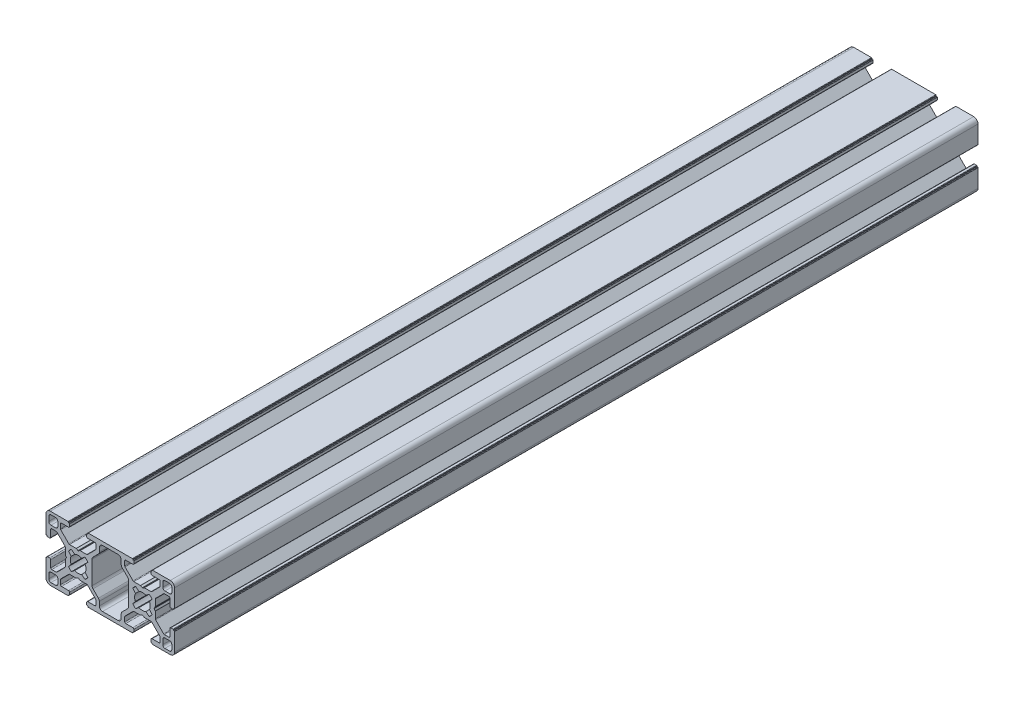
SolidWorks part; units mm, degrees
ref_plane "Front Plane" through (0, 0, 0) normal (0, 0, 1) x (1, 0, 0)
ref_plane "Top Plane" through (0, 0, 0) normal (0, 1, 0) x (1, 0, 0)
ref_plane "Right Plane" through (0, 0, 0) normal (1, 0, 0) x (0, 0, -1)
ref_plane "Plano1" through (0, 0, 1000) normal (0, 0, 1) x (1, 0, 0)
sketch "Croquis1" plane through (0, 0, 1000) normal (0, 0, 1) x (1, 0, 0)
  line L0 (-18.4, -4.5) -> (-18.4, -2.3)
  line L1 (-17.4, -1.3) -> (-15.2, -1.3)
  line L2 (-14.2, -2.3) -> (-14.2, -4.5)
  line L3 (-15.2, -5.5) -> (-17.4, -5.5)
  line L4 (-18.4, -27.7) -> (-18.4, -25.5)
  line L5 (-17.4, -24.5) -> (-15.2, -24.5)
  line L6 (-14.2, -25.5) -> (-14.2, -27.7)
  line L7 (-15.2, -28.7) -> (-17.4, -28.7)
  line L8 (35.8, -1.3) -> (38, -1.3)
  line L9 (39, -2.3) -> (39, -4.5)
  line L10 (38, -5.5) -> (35.8, -5.5)
  line L11 (34.8, -4.5) -> (34.8, -2.3)
  line L12 (35.8, -24.5) -> (38, -24.5)
  line L13 (39, -25.5) -> (39, -27.7)
  line L14 (38, -28.7) -> (35.8, -28.7)
  line L15 (34.8, -27.7) -> (34.8, -25.5)
  line L16 (-0.1816, -11.8641) -> (-1.4194, -13.3999)
  line L17 (-1.4194, -16.6001) -> (-0.1816, -18.1359)
  line L18 (-1.5453, -19.5053) -> (-3.0999, -18.2806)
  line L19 (-6.3001, -18.2806) -> (-7.8547, -19.5053)
  line L20 (-9.2184, -18.1359) -> (-7.9806, -16.6001)
  line L21 (-7.9806, -13.3999) -> (-9.2184, -11.8641)
  line L22 (-7.8547, -10.4947) -> (-6.3001, -11.7194)
  line L23 (-3.0999, -11.7194) -> (-1.5453, -10.4947)
  line L24 (20.7816, -18.1359) -> (22.0194, -16.6001)
  line L25 (22.0194, -13.3999) -> (20.7816, -11.8641)
  line L26 (22.1453, -10.4947) -> (23.6999, -11.7194)
  line L27 (26.9001, -11.7194) -> (28.4547, -10.4947)
  line L28 (29.8184, -11.8641) -> (28.5806, -13.3999)
  line L29 (28.5806, -16.6001) -> (29.8184, -18.1359)
  line L30 (28.4547, -19.5053) -> (26.9001, -18.2806)
  line L31 (23.6999, -18.2806) -> (22.1453, -19.5053)
  line L32 (18.7955, -9.6503) -> (18.7955, -20.3497)
  line L33 (18.3562, -21.4104) -> (15.8393, -23.9272)
  line L34 (15.4, -24.9879) -> (15.4, -26.85)
  line L35 (13.9, -28.35) -> (6.7, -28.35)
  line L36 (5.2, -26.85) -> (5.2, -24.9879)
  line L37 (4.7607, -23.9272) -> (2.2438, -21.4104)
  line L38 (1.8045, -20.3497) -> (1.8045, -9.6503)
  line L39 (2.2438, -8.5896) -> (4.7607, -6.0728)
  line L40 (5.2, -5.0121) -> (5.2, -3.15)
  line L41 (6.7, -1.65) -> (13.9, -1.65)
  line L42 (15.4, -3.15) -> (15.4, -5.0121)
  line L43 (15.8393, -6.0728) -> (18.3562, -8.5896)
  line L44 (-8.9, -0.5) -> (-9.2, -0.5)
  line L45 (-9.2, -0.5) -> (-9.2, -0.2)
  line L46 (-9.4, 0) -> (-17.7, 0)
  line L47 (-19.7, -2) -> (-19.7, -10.3)
  line L48 (-19.5, -10.5) -> (-19.2, -10.5)
  line L49 (-19.2, -10.5) -> (-19.2, -10.8)
  line L50 (-19, -11) -> (-18, -11)
  line L51 (-17.5, -10.5) -> (-17.5, -7.25)
  line L52 (-17, -6.75) -> (-14.9569, -6.75)
  line L53 (-14.6036, -6.8963) -> (-10.8466, -10.6491)
  line L54 (-10.7, -11.0028) -> (-10.7, -14.0468)
  line L55 (-10.6736, -14.1462) -> (-10.2417, -14.9006)
  line L56 (-10.2417, -15.0994) -> (-10.6736, -15.8538)
  line L57 (-10.7, -15.9532) -> (-10.7, -18.9972)
  line L58 (-10.8466, -19.3509) -> (-14.6036, -23.1037)
  line L59 (-14.9569, -23.25) -> (-17, -23.25)
  line L60 (-17.5, -22.75) -> (-17.5, -19.5)
  line L61 (-18, -19) -> (-19, -19)
  line L62 (-19.2, -19.2) -> (-19.2, -19.5)
  line L63 (-19.2, -19.5) -> (-19.5, -19.5)
  line L64 (-19.7, -19.7) -> (-19.7, -28)
  line L65 (-17.7, -30) -> (-9.4, -30)
  line L66 (-9.2, -29.8) -> (-9.2, -29.5)
  line L67 (-9.2, -29.5) -> (-8.9, -29.5)
  line L68 (-8.7, -29.3) -> (-8.7, -28.3)
  line L69 (-9.2, -27.8) -> (-12.45, -27.8)
  line L70 (-12.95, -27.3) -> (-12.95, -25.2571)
  line L71 (-12.8036, -24.9036) -> (-9.0509, -21.1509)
  line L72 (-8.6974, -21.0045) -> (-5.6536, -21.0045)
  line L73 (-5.5536, -20.9777) -> (-4.8, -20.5426)
  line L74 (-4.6, -20.5426) -> (-3.8464, -20.9777)
  line L75 (-3.7464, -21.0045) -> (-0.7026, -21.0045)
  line L76 (-0.3491, -21.1509) -> (3.4036, -24.9036)
  line L77 (3.55, -25.2571) -> (3.55, -27.3)
  line L78 (3.05, -27.8) -> (-0.2, -27.8)
  line L79 (-0.7, -28.3) -> (-0.7, -29.3)
  line L80 (-0.5, -29.5) -> (-0.2, -29.5)
  line L81 (-0.2, -29.5) -> (-0.2, -29.8)
  line L82 (0, -30) -> (20.6, -30)
  line L83 (20.8, -29.8) -> (20.8, -29.5)
  line L84 (20.8, -29.5) -> (21.1, -29.5)
  line L85 (21.3, -29.3) -> (21.3, -28.3)
  line L86 (20.8, -27.8) -> (17.55, -27.8)
  line L87 (17.05, -27.3) -> (17.05, -25.2571)
  line L88 (17.1964, -24.9036) -> (20.9491, -21.1509)
  line L89 (21.3026, -21.0045) -> (24.3464, -21.0045)
  line L90 (24.4464, -20.9777) -> (25.2, -20.5426)
  line L91 (25.4, -20.5426) -> (26.1536, -20.9777)
  line L92 (26.2536, -21.0045) -> (29.2974, -21.0045)
  line L93 (29.6509, -21.1509) -> (33.4036, -24.9036)
  line L94 (33.55, -25.2571) -> (33.55, -27.3)
  line L95 (33.05, -27.8) -> (29.8, -27.8)
  line L96 (29.3, -28.3) -> (29.3, -29.3)
  line L97 (29.5, -29.5) -> (29.8, -29.5)
  line L98 (29.8, -29.5) -> (29.8, -29.8)
  line L99 (30, -30) -> (38.3, -30)
  line L100 (40.3, -28) -> (40.3, -19.7)
  line L101 (40.1, -19.5) -> (39.8, -19.5)
  line L102 (39.8, -19.5) -> (39.8, -19.2)
  line L103 (39.6, -19) -> (38.6, -19)
  line L104 (38.1, -19.5) -> (38.1, -22.75)
  line L105 (37.6, -23.25) -> (35.5569, -23.25)
  line L106 (35.2036, -23.1037) -> (31.4466, -19.3509)
  line L107 (31.3, -18.9972) -> (31.3, -15.9532)
  line L108 (31.2736, -15.8538) -> (30.8417, -15.0994)
  line L109 (30.8417, -14.9006) -> (31.2736, -14.1462)
  line L110 (31.3, -14.0468) -> (31.3, -11.0028)
  line L111 (31.4466, -10.6491) -> (35.2036, -6.8963)
  line L112 (35.5569, -6.75) -> (37.6, -6.75)
  line L113 (38.1, -7.25) -> (38.1, -10.5)
  line L114 (38.6, -11) -> (39.6, -11)
  line L115 (39.8, -10.8) -> (39.8, -10.5)
  line L116 (39.8, -10.5) -> (40.1, -10.5)
  line L117 (40.3, -10.3) -> (40.3, -2)
  line L118 (38.3, 0) -> (30, 0)
  line L119 (29.8, -0.2) -> (29.8, -0.5)
  line L120 (29.8, -0.5) -> (29.5, -0.5)
  line L121 (29.3, -0.7) -> (29.3, -1.7)
  line L122 (29.8, -2.2) -> (33.05, -2.2)
  line L123 (33.55, -2.7) -> (33.55, -4.7429)
  line L124 (33.4036, -5.0964) -> (29.6509, -8.8491)
  line L125 (29.2974, -8.9955) -> (26.2536, -8.9955)
  line L126 (26.1536, -9.0223) -> (25.4, -9.4574)
  line L127 (25.2, -9.4574) -> (24.4464, -9.0223)
  line L128 (24.3464, -8.9955) -> (21.3026, -8.9955)
  line L129 (20.9491, -8.8491) -> (17.1964, -5.0964)
  line L130 (17.05, -4.7429) -> (17.05, -2.7)
  line L131 (17.55, -2.2) -> (20.8, -2.2)
  line L132 (21.3, -1.7) -> (21.3, -0.7)
  line L133 (21.1, -0.5) -> (20.8, -0.5)
  line L134 (20.8, -0.5) -> (20.8, -0.2)
  line L135 (20.6, 0) -> (0, 0)
  line L136 (-0.2, -0.2) -> (-0.2, -0.5)
  line L137 (-0.2, -0.5) -> (-0.5, -0.5)
  line L138 (-0.7, -0.7) -> (-0.7, -1.7)
  line L139 (-0.2, -2.2) -> (3.05, -2.2)
  line L140 (3.55, -2.7) -> (3.55, -4.7429)
  line L141 (3.4036, -5.0964) -> (-0.3491, -8.8491)
  line L142 (-0.7026, -8.9955) -> (-3.7464, -8.9955)
  line L143 (-3.8464, -9.0223) -> (-4.6, -9.4574)
  line L144 (-4.8, -9.4574) -> (-5.5536, -9.0223)
  line L145 (-5.6536, -8.9955) -> (-8.6974, -8.9955)
  line L146 (-9.0509, -8.8491) -> (-12.8036, -5.0964)
  line L147 (-12.95, -4.7429) -> (-12.95, -2.7)
  line L148 (-12.45, -2.2) -> (-9.2, -2.2)
  line L149 (-8.7, -1.7) -> (-8.7, -0.7)
  arc A0 (-17.4, -5.5) -> (-18.4, -4.5) centre (-17.4, -4.5) cw
  arc A1 (-18.4, -2.3) -> (-17.4, -1.3) centre (-17.4, -2.3) cw
  arc A2 (-15.2, -1.3) -> (-14.2, -2.3) centre (-15.2, -2.3) cw
  arc A3 (-14.2, -4.5) -> (-15.2, -5.5) centre (-15.2, -4.5) cw
  arc A4 (-17.4, -28.7) -> (-18.4, -27.7) centre (-17.4, -27.7) cw
  arc A5 (-18.4, -25.5) -> (-17.4, -24.5) centre (-17.4, -25.5) cw
  arc A6 (-15.2, -24.5) -> (-14.2, -25.5) centre (-15.2, -25.5) cw
  arc A7 (-14.2, -27.7) -> (-15.2, -28.7) centre (-15.2, -27.7) cw
  arc A8 (34.8, -2.3) -> (35.8, -1.3) centre (35.8, -2.3) cw
  arc A9 (38, -1.3) -> (39, -2.3) centre (38, -2.3) cw
  arc A10 (39, -4.5) -> (38, -5.5) centre (38, -4.5) cw
  arc A11 (35.8, -5.5) -> (34.8, -4.5) centre (35.8, -4.5) cw
  arc A12 (34.8, -25.5) -> (35.8, -24.5) centre (35.8, -25.5) cw
  arc A13 (38, -24.5) -> (39, -25.5) centre (38, -25.5) cw
  arc A14 (39, -27.7) -> (38, -28.7) centre (38, -27.7) cw
  arc A15 (35.8, -28.7) -> (34.8, -27.7) centre (35.8, -27.7) cw
  arc A16 (-1.5453, -10.4947) -> (-0.1816, -11.8641) centre (-4.7, -15) cw
  arc A17 (-1.4194, -13.3999) -> (-1.4194, -16.6001) centre (-4.7, -15) cw
  arc A18 (-0.1816, -18.1359) -> (-1.5453, -19.5053) centre (-4.7, -15) cw
  arc A19 (-3.0999, -18.2806) -> (-6.3001, -18.2806) centre (-4.7, -15) cw
  arc A20 (-7.8547, -19.5053) -> (-9.2184, -18.1359) centre (-4.7, -15) cw
  arc A21 (-7.9806, -16.6001) -> (-7.9806, -13.3999) centre (-4.7, -15) cw
  arc A22 (-9.2184, -11.8641) -> (-7.8547, -10.4947) centre (-4.7, -15) cw
  arc A23 (-6.3001, -11.7194) -> (-3.0999, -11.7194) centre (-4.7, -15) cw
  arc A24 (22.1453, -19.5053) -> (20.7816, -18.1359) centre (25.3, -15) cw
  arc A25 (22.0194, -16.6001) -> (22.0194, -13.3999) centre (25.3, -15) cw
  arc A26 (20.7816, -11.8641) -> (22.1453, -10.4947) centre (25.3, -15) cw
  arc A27 (23.6999, -11.7194) -> (26.9001, -11.7194) centre (25.3, -15) cw
  arc A28 (28.4547, -10.4947) -> (29.8184, -11.8641) centre (25.3, -15) cw
  arc A29 (28.5806, -13.3999) -> (28.5806, -16.6001) centre (25.3, -15) cw
  arc A30 (29.8184, -18.1359) -> (28.4547, -19.5053) centre (25.3, -15) cw
  arc A31 (26.9001, -18.2806) -> (23.6999, -18.2806) centre (25.3, -15) cw
  arc A32 (18.3562, -8.5896) -> (18.7955, -9.6503) centre (17.2955, -9.6503) cw
  arc A33 (18.7955, -20.3497) -> (18.3562, -21.4104) centre (17.2955, -20.3497) cw
  arc A34 (15.8393, -23.9272) -> (15.4, -24.9879) centre (16.9, -24.9879) ccw
  arc A35 (15.4, -26.85) -> (13.9, -28.35) centre (13.9, -26.85) cw
  arc A36 (6.7, -28.35) -> (5.2, -26.85) centre (6.7, -26.85) cw
  arc A37 (5.2, -24.9879) -> (4.7607, -23.9272) centre (3.7, -24.9879) ccw
  arc A38 (2.2438, -21.4104) -> (1.8045, -20.3497) centre (3.3045, -20.3497) cw
  arc A39 (1.8045, -9.6503) -> (2.2438, -8.5896) centre (3.3045, -9.6503) cw
  arc A40 (4.7607, -6.0728) -> (5.2, -5.0121) centre (3.7, -5.0121) ccw
  arc A41 (5.2, -3.15) -> (6.7, -1.65) centre (6.7, -3.15) cw
  arc A42 (13.9, -1.65) -> (15.4, -3.15) centre (13.9, -3.15) cw
  arc A43 (15.4, -5.0121) -> (15.8393, -6.0728) centre (16.9, -5.0121) ccw
  arc A44 (-8.7, -0.7) -> (-8.9, -0.5) centre (-8.9, -0.7) ccw
  arc A45 (-9.2, -0.2) -> (-9.4, 0) centre (-9.4, -0.2) ccw
  arc A46 (-17.7, 0) -> (-19.7, -2) centre (-17.7, -2) ccw
  arc A47 (-19.7, -10.3) -> (-19.5, -10.5) centre (-19.5, -10.3) ccw
  arc A48 (-19.2, -10.8) -> (-19, -11) centre (-19, -10.8) ccw
  arc A49 (-18, -11) -> (-17.5, -10.5) centre (-18, -10.5) ccw
  arc A50 (-17.5, -7.25) -> (-17, -6.75) centre (-17, -7.25) cw
  arc A51 (-14.9569, -6.75) -> (-14.6036, -6.8963) centre (-14.9569, -7.25) cw
  arc A52 (-10.8466, -10.6491) -> (-10.7, -11.0028) centre (-11.2, -11.0028) cw
  arc A53 (-10.7, -14.0468) -> (-10.6736, -14.1462) centre (-10.5, -14.0468) ccw
  arc A54 (-10.2417, -14.9006) -> (-10.2417, -15.0994) centre (-10.4153, -15) cw
  arc A55 (-10.6736, -15.8538) -> (-10.7, -15.9532) centre (-10.5, -15.9532) ccw
  arc A56 (-10.7, -18.9972) -> (-10.8466, -19.3509) centre (-11.2, -18.9972) cw
  arc A57 (-14.6036, -23.1037) -> (-14.9569, -23.25) centre (-14.9569, -22.75) cw
  arc A58 (-17, -23.25) -> (-17.5, -22.75) centre (-17, -22.75) cw
  arc A59 (-17.5, -19.5) -> (-18, -19) centre (-18, -19.5) ccw
  arc A60 (-19, -19) -> (-19.2, -19.2) centre (-19, -19.2) ccw
  arc A61 (-19.5, -19.5) -> (-19.7, -19.7) centre (-19.5, -19.7) ccw
  arc A62 (-19.7, -28) -> (-17.7, -30) centre (-17.7, -28) ccw
  arc A63 (-9.4, -30) -> (-9.2, -29.8) centre (-9.4, -29.8) ccw
  arc A64 (-8.9, -29.5) -> (-8.7, -29.3) centre (-8.9, -29.3) ccw
  arc A65 (-8.7, -28.3) -> (-9.2, -27.8) centre (-9.2, -28.3) ccw
  arc A66 (-12.45, -27.8) -> (-12.95, -27.3) centre (-12.45, -27.3) cw
  arc A67 (-12.95, -25.2571) -> (-12.8036, -24.9036) centre (-12.45, -25.2571) cw
  arc A68 (-9.0509, -21.1509) -> (-8.6974, -21.0045) centre (-8.6974, -21.5045) cw
  arc A69 (-5.6536, -21.0045) -> (-5.5536, -20.9777) centre (-5.6536, -20.8045) ccw
  arc A70 (-4.8, -20.5426) -> (-4.6, -20.5426) centre (-4.7, -20.7158) cw
  arc A71 (-3.8464, -20.9777) -> (-3.7464, -21.0045) centre (-3.7464, -20.8045) ccw
  arc A72 (-0.7026, -21.0045) -> (-0.3491, -21.1509) centre (-0.7026, -21.5045) cw
  arc A73 (3.4036, -24.9036) -> (3.55, -25.2571) centre (3.05, -25.2571) cw
  arc A74 (3.55, -27.3) -> (3.05, -27.8) centre (3.05, -27.3) cw
  arc A75 (-0.2, -27.8) -> (-0.7, -28.3) centre (-0.2, -28.3) ccw
  arc A76 (-0.7, -29.3) -> (-0.5, -29.5) centre (-0.5, -29.3) ccw
  arc A77 (-0.2, -29.8) -> (0, -30) centre (0, -29.8) ccw
  arc A78 (20.6, -30) -> (20.8, -29.8) centre (20.6, -29.8) ccw
  arc A79 (21.1, -29.5) -> (21.3, -29.3) centre (21.1, -29.3) ccw
  arc A80 (21.3, -28.3) -> (20.8, -27.8) centre (20.8, -28.3) ccw
  arc A81 (17.55, -27.8) -> (17.05, -27.3) centre (17.55, -27.3) cw
  arc A82 (17.05, -25.2571) -> (17.1964, -24.9036) centre (17.55, -25.2571) cw
  arc A83 (20.9491, -21.1509) -> (21.3026, -21.0045) centre (21.3026, -21.5045) cw
  arc A84 (24.3464, -21.0045) -> (24.4464, -20.9777) centre (24.3464, -20.8045) ccw
  arc A85 (25.2, -20.5426) -> (25.4, -20.5426) centre (25.3, -20.7158) cw
  arc A86 (26.1536, -20.9777) -> (26.2536, -21.0045) centre (26.2536, -20.8045) ccw
  arc A87 (29.2974, -21.0045) -> (29.6509, -21.1509) centre (29.2974, -21.5045) cw
  arc A88 (33.4036, -24.9036) -> (33.55, -25.2571) centre (33.05, -25.2571) cw
  arc A89 (33.55, -27.3) -> (33.05, -27.8) centre (33.05, -27.3) cw
  arc A90 (29.8, -27.8) -> (29.3, -28.3) centre (29.8, -28.3) ccw
  arc A91 (29.3, -29.3) -> (29.5, -29.5) centre (29.5, -29.3) ccw
  arc A92 (29.8, -29.8) -> (30, -30) centre (30, -29.8) ccw
  arc A93 (38.3, -30) -> (40.3, -28) centre (38.3, -28) ccw
  arc A94 (40.3, -19.7) -> (40.1, -19.5) centre (40.1, -19.7) ccw
  arc A95 (39.8, -19.2) -> (39.6, -19) centre (39.6, -19.2) ccw
  arc A96 (38.6, -19) -> (38.1, -19.5) centre (38.6, -19.5) ccw
  arc A97 (38.1, -22.75) -> (37.6, -23.25) centre (37.6, -22.75) cw
  arc A98 (35.5569, -23.25) -> (35.2036, -23.1037) centre (35.5569, -22.75) cw
  arc A99 (31.4466, -19.3509) -> (31.3, -18.9972) centre (31.8, -18.9972) cw
  arc A100 (31.3, -15.9532) -> (31.2736, -15.8538) centre (31.1, -15.9532) ccw
  arc A101 (30.8417, -15.0994) -> (30.8417, -14.9006) centre (31.0153, -15) cw
  arc A102 (31.2736, -14.1462) -> (31.3, -14.0468) centre (31.1, -14.0468) ccw
  arc A103 (31.3, -11.0028) -> (31.4466, -10.6491) centre (31.8, -11.0028) cw
  arc A104 (35.2036, -6.8963) -> (35.5569, -6.75) centre (35.5569, -7.25) cw
  arc A105 (37.6, -6.75) -> (38.1, -7.25) centre (37.6, -7.25) cw
  arc A106 (38.1, -10.5) -> (38.6, -11) centre (38.6, -10.5) ccw
  arc A107 (39.6, -11) -> (39.8, -10.8) centre (39.6, -10.8) ccw
  arc A108 (40.1, -10.5) -> (40.3, -10.3) centre (40.1, -10.3) ccw
  arc A109 (40.3, -2) -> (38.3, 0) centre (38.3, -2) ccw
  arc A110 (30, 0) -> (29.8, -0.2) centre (30, -0.2) ccw
  arc A111 (29.5, -0.5) -> (29.3, -0.7) centre (29.5, -0.7) ccw
  arc A112 (29.3, -1.7) -> (29.8, -2.2) centre (29.8, -1.7) ccw
  arc A113 (33.05, -2.2) -> (33.55, -2.7) centre (33.05, -2.7) cw
  arc A114 (33.55, -4.7429) -> (33.4036, -5.0964) centre (33.05, -4.7429) cw
  arc A115 (29.6509, -8.8491) -> (29.2974, -8.9955) centre (29.2974, -8.4955) cw
  arc A116 (26.2536, -8.9955) -> (26.1536, -9.0223) centre (26.2536, -9.1955) ccw
  arc A117 (25.4, -9.4574) -> (25.2, -9.4574) centre (25.3, -9.2842) cw
  arc A118 (24.4464, -9.0223) -> (24.3464, -8.9955) centre (24.3464, -9.1955) ccw
  arc A119 (21.3026, -8.9955) -> (20.9491, -8.8491) centre (21.3026, -8.4955) cw
  arc A120 (17.1964, -5.0964) -> (17.05, -4.7429) centre (17.55, -4.7429) cw
  arc A121 (17.05, -2.7) -> (17.55, -2.2) centre (17.55, -2.7) cw
  arc A122 (20.8, -2.2) -> (21.3, -1.7) centre (20.8, -1.7) ccw
  arc A123 (21.3, -0.7) -> (21.1, -0.5) centre (21.1, -0.7) ccw
  arc A124 (20.8, -0.2) -> (20.6, 0) centre (20.6, -0.2) ccw
  arc A125 (0, 0) -> (-0.2, -0.2) centre (0, -0.2) ccw
  arc A126 (-0.5, -0.5) -> (-0.7, -0.7) centre (-0.5, -0.7) ccw
  arc A127 (-0.7, -1.7) -> (-0.2, -2.2) centre (-0.2, -1.7) ccw
  arc A128 (3.05, -2.2) -> (3.55, -2.7) centre (3.05, -2.7) cw
  arc A129 (3.55, -4.7429) -> (3.4036, -5.0964) centre (3.05, -4.7429) cw
  arc A130 (-0.3491, -8.8491) -> (-0.7026, -8.9955) centre (-0.7026, -8.4955) cw
  arc A131 (-3.7464, -8.9955) -> (-3.8464, -9.0223) centre (-3.7464, -9.1955) ccw
  arc A132 (-4.6, -9.4574) -> (-4.8, -9.4574) centre (-4.7, -9.2842) cw
  arc A133 (-5.5536, -9.0223) -> (-5.6536, -8.9955) centre (-5.6536, -9.1955) ccw
  arc A134 (-8.6974, -8.9955) -> (-9.0509, -8.8491) centre (-8.6974, -8.4955) cw
  arc A135 (-12.8036, -5.0964) -> (-12.95, -4.7429) centre (-12.45, -4.7429) cw
  arc A136 (-12.95, -2.7) -> (-12.45, -2.2) centre (-12.45, -2.7) cw
  arc A137 (-9.2, -2.2) -> (-8.7, -1.7) centre (-9.2, -1.7) ccw
extrude "Saliente-Extruir1" add sketch "Croquis1" against normal blind 375
